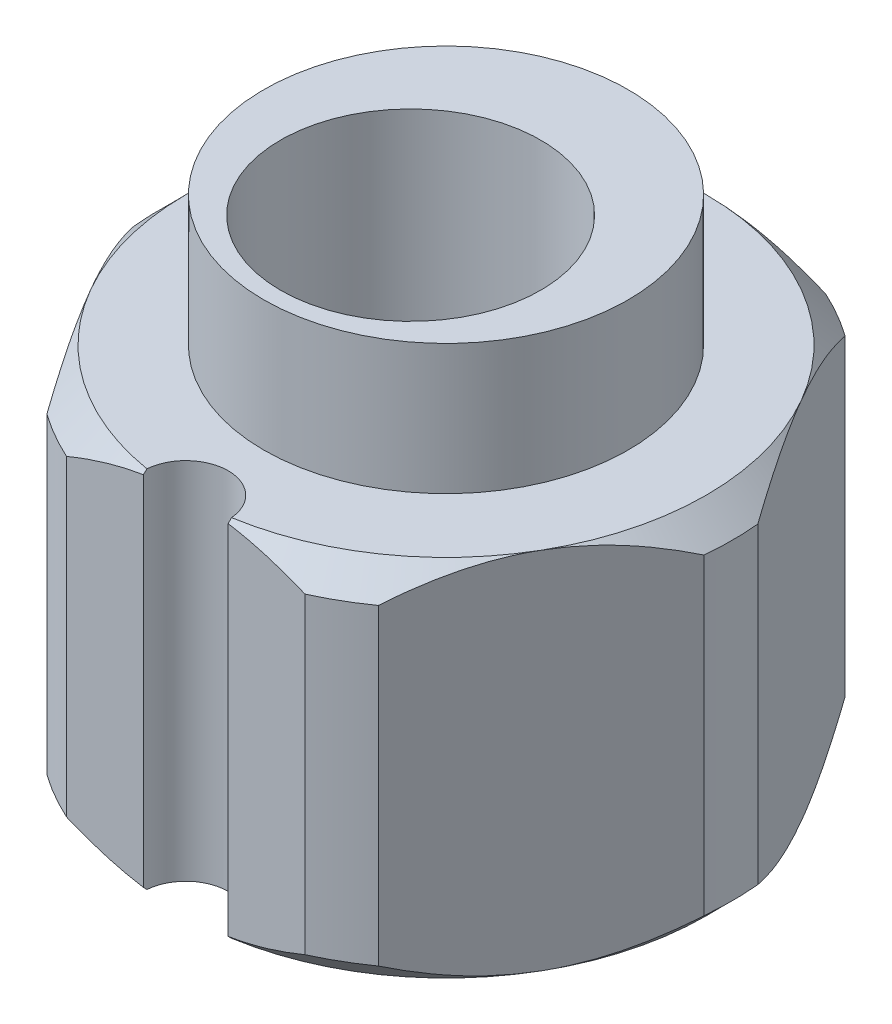
SolidWorks part; units mm, degrees
ref_plane "Front Plane" through (0, 0, 0) normal (0, 0, 1) x (1, 0, 0)
ref_plane "Top Plane" through (0, 0, 0) normal (0, 1, 0) x (1, 0, 0)
ref_plane "Right Plane" through (0, 0, 0) normal (1, 0, 0) x (0, 0, -1)
sketch "Sketch2" plane through (0, 0, 0) normal (0, 1, 0) x (1, 0, 0)
  circle A0 centre (0, 0) radius 5.5
  dimension "D1" = 11
extrude "Boss-Extrude2" add sketch "Sketch2" along normal blind 7
chamfer "Chamfer1" distance 0.5 angle 45 2 edges at (0, 0, 5.5) (0, 7, 5.5)
sketch "Sketch3" plane through (0, 7, 0) normal (0, 1, 0) x (1, 0, 0)
  line L1 (5.7735, 0) -> (2.8868, 5)
  line L2 (2.8868, 5) -> (-2.8868, 5)
  line L3 (-2.8868, 5) -> (-5.7735, 0)
  line L4 (-5.7735, 0) -> (-2.8868, -5)
  line L5 (-2.8868, -5) -> (2.8868, -5)
  line L6 (2.8868, -5) -> (5.7735, 0)
  circle A0 centre (0, 0) radius 5 construction
  circle A1 centre (0, 0) radius 7.5
  dimension "D1" = 10
  dimension "D2" = 15
extrude "Cut-Extrude1" cut sketch "Sketch3" against normal through all
sketch "Sketch4" plane through (0, 7, 0) normal (0, 1, 0) x (1, 0, 0)
  line L0 (-0.815, -5) -> (0.815, -5)
  circle A0 centre (0, -5) radius 0.815 construction
  arc A1 (-0.815, -5) -> (0.815, -5) centre (0, -5) cw
  dimension "D1" = 1.63
extrude "Cut-Extrude2" cut sketch "Sketch4" against normal through all
sketch "Sketch5" plane through (0, 7, 0) normal (0, 1, 0) x (1, 0, 0)
  circle A0 centre (0, 0) radius 3.5
  dimension "D1" = 7
extrude "Boss-Extrude3" add sketch "Sketch5" along normal blind 2.5
sketch "Sketch6" plane through (0, 9.5, 0) normal (0, 1, 0) x (1, 0, 0)
  circle A0 centre (0, -0.68) radius 2.5
  point P2 (0, 0)
  dimension "D2" = 5
  dimension "D1" = 0.68
extrude "Cut-Extrude3" cut sketch "Sketch6" against normal through all
